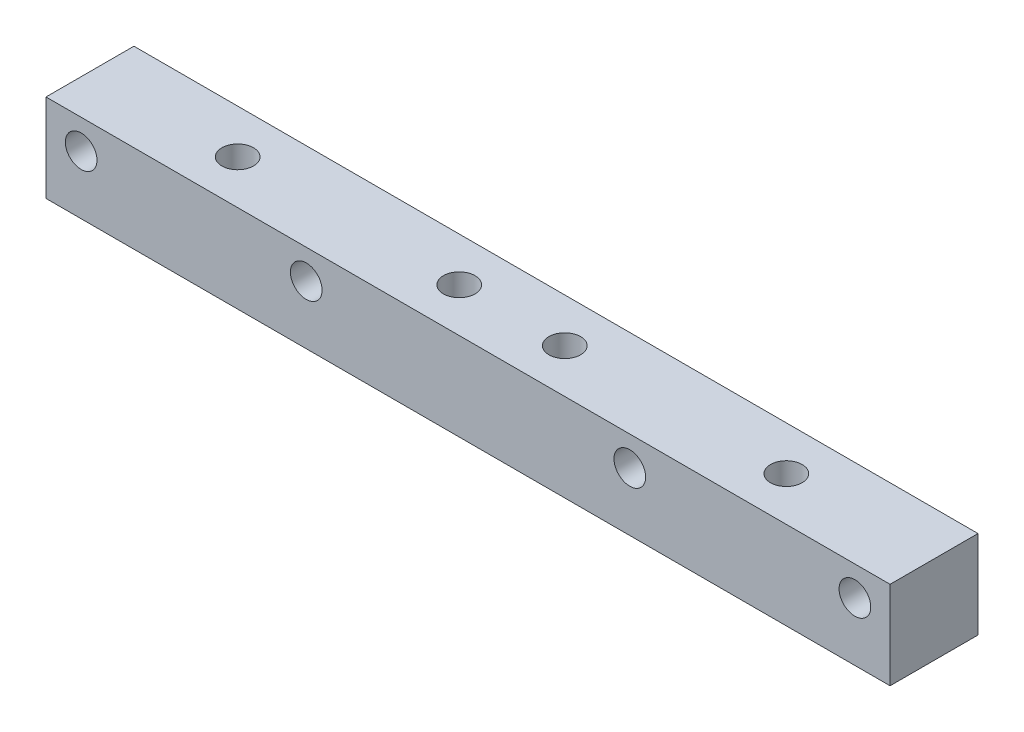
SolidWorks part; units mm, degrees
material "6061 Alloy"
ref_plane "Front Plane" through (0, 0, 0) normal (0, 0, 1) x (1, 0, 0)
ref_plane "Top Plane" through (0, 0, 0) normal (0, 1, 0) x (1, 0, 0)
ref_plane "Right Plane" through (0, 0, 0) normal (1, 0, 0) x (0, 0, -1)
sketch "Sketch1" plane through (0, 0, 0) normal (1, 0, 0) x (0, 0, -1)
  line L1 (-6.25, -6.25) -> (6.25, -6.25)
  line L2 (-6.25, -6.25) -> (-6.25, 6.25)
  line L3 (-6.25, 6.25) -> (6.25, 6.25)
  line L4 (6.25, -6.25) -> (6.25, 6.25)
  line L5 (-6.25, -6.25) -> (6.25, 6.25) construction
  line L6 (-6.25, 6.25) -> (6.25, -6.25) construction
  point P0 (0, 0)
  dimension "D1" = 12.5
extrude "Boss-Extrude1" add sketch "Sketch1" along normal mid plane 120
hole_wizard "Ø4.0mm Dowel Hole1" positions "Sketch2" profile "Sketch3" hole size "Ø4.0" standard "ANSI Metric" end condition through all
sketch "Sketch2" plane through (0, 0, 6.25) normal (0, 0, 1) x (1, 0, 0)
  line L0 (-55, 2.07) -> (-23, 2.07) construction
  line L1 (-23, 2.07) -> (23, 2.07) construction
  line L2 (23, 2.07) -> (55, 2.07) construction
  line L5 (-60, 6.25) -> (-60, -6.25) construction
  line L6 (60, -6.25) -> (-60, -6.25) construction
  line L7 (60, 6.25) -> (60, -6.25) construction
  point P0 (-55, 2.07)
  point P2 (-23, 2.07)
  point P4 (23, 2.07)
  point P6 (55, 2.07)
  dimension "D1" = 32
  dimension "D2" = 5
  dimension "D3" = 8.32
  dimension "D4" = 5
sketch "Sketch3" plane through (-55, 2.07, 6.25) normal (1, 0, 0) x (0, -1, 0)
  line L0 (0, 0) -> (0, 12.5)
  line L1 (0, 12.5) -> (2.25, 12.5)
  line L2 (2.25, 12.5) -> (2.25, 0)
  line L5 (2.25, 0) -> (0, 0)
  line L11 (0, -6.35) -> (0, 107.95) construction
  dimension "Thru Hole Dia." = 4.5
  dimension "Thru Hole Depth" = 12.5
hole_wizard "Ø1.0mm Dowel Hole1" positions "Sketch4" profile "Sketch5" hole size "Ø1.0" standard "ANSI Metric" end condition through all
sketch "Sketch4" plane through (0, 6.25, 0) normal (0, 1, 0) x (1, 0, 0)
  line L0 (-60, 6.25) -> (-60, -6.25) construction
  line L1 (60, 6.25) -> (60, -6.25) construction
  point P0 (-39, 0)
  point P5 (39, 0)
  point P14 (-7.5, 0)
  point P16 (7.5, 0)
  dimension "D1" = 21
  dimension "D2" = 21
  dimension "D3" = 15
  dimension "D4" = 7.5
sketch "Sketch5" plane through (-39, 6.25, 0) normal (1, 0, 0) x (0, 0, 1)
  line L0 (0, 0) -> (0, 12.5)
  line L1 (0, 12.5) -> (2.25, 12.5)
  line L2 (2.25, 12.5) -> (2.25, 0)
  line L5 (2.25, 0) -> (0, 0)
  line L11 (0, -6.35) -> (0, 107.95) construction
  dimension "Thru Hole Dia." = 4.5
  dimension "Thru Hole Depth" = 12.5
equation "\"D1@Sketch4\"=(32/2)+5"
equation "\"D2@Sketch4\"=\"D1@Sketch4\""
equation "\"D4@Sketch4\"=\"D3@Sketch4\"/2"
